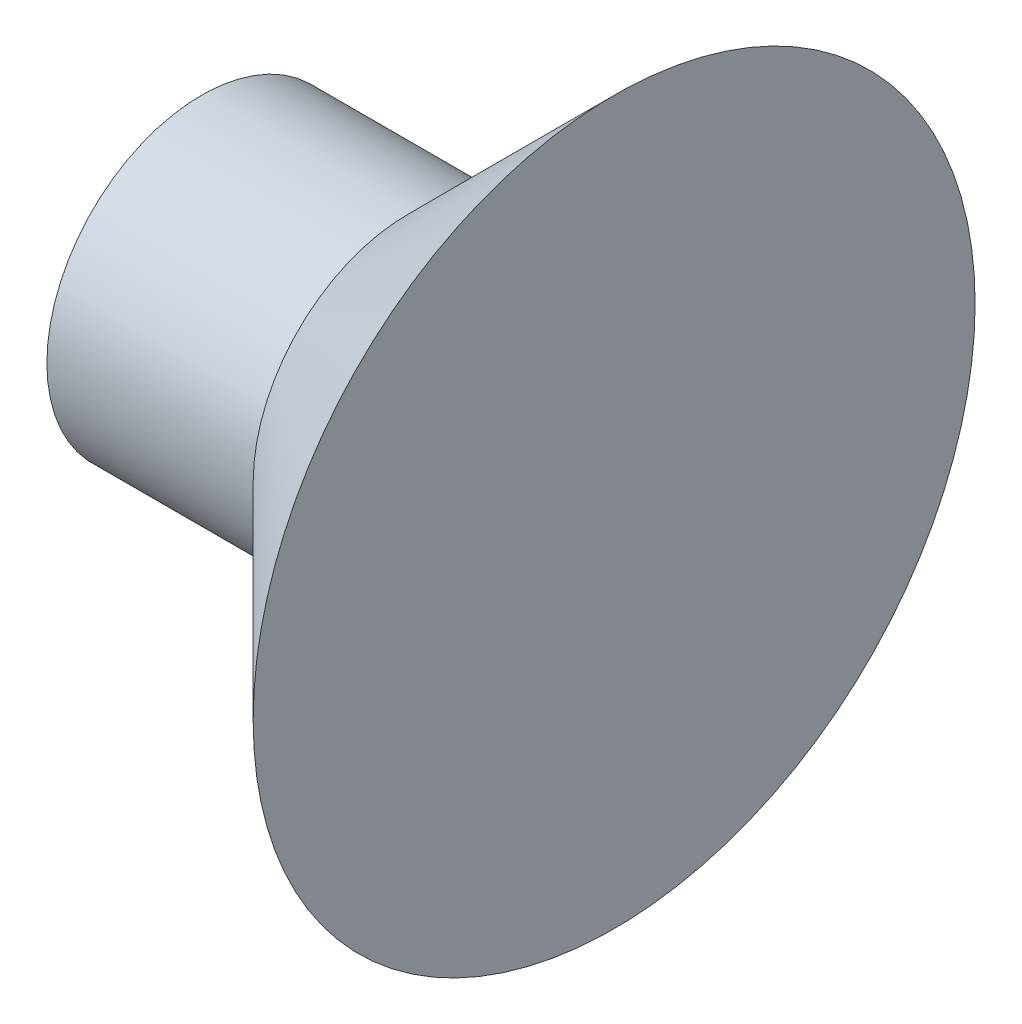
SolidWorks part; units mm, degrees
ref_plane "Plan de face" through (0, 0, 0) normal (0, 0, 1) x (1, 0, 0)
ref_plane "Plan de dessus" through (0, 0, 0) normal (0, 1, 0) x (1, 0, 0)
ref_plane "Plan de droite" through (0, 0, 0) normal (1, 0, 0) x (0, 0, -1)
sketch "Esquisse1" plane through (0, 0, 0) normal (0, 0, 1) x (1, 0, 0)
  line L0 (0, 0) -> (-4, 0)
  line L1 (-4, 0) -> (-4, 1.5)
  line L2 (-4, 1.5) -> (-2, 1.5)
  line L3 (-2, 1.5) -> (0, 3.5)
  line L4 (0, 3.5) -> (0, 0)
  line L5 (0, 0) -> (21.1509, 0) construction
  dimension "D1" = 45
  dimension "D2" = 2
  dimension "D3" = 3
  dimension "D4" = 4
revolve "Révolution1" add sketch "Esquisse1" angle 360 about L5
